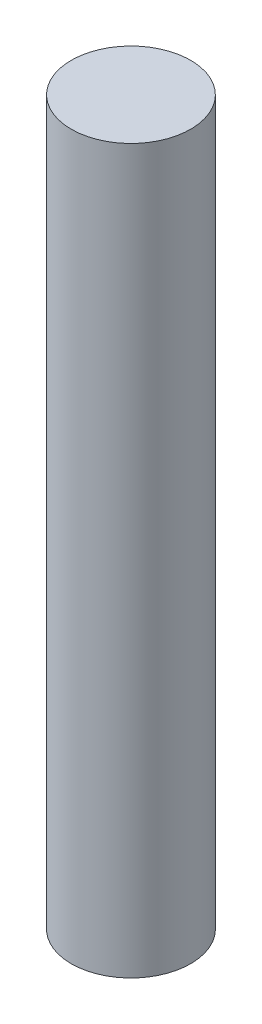
SolidWorks part; units mm, degrees
ref_plane "Front Plane" through (0, 0, 0) normal (0, 0, 1) x (1, 0, 0)
ref_plane "Top Plane" through (0, 0, 0) normal (0, 1, 0) x (1, 0, 0)
ref_plane "Right Plane" through (0, 0, 0) normal (1, 0, 0) x (0, 0, -1)
sketch "Sketch1" plane through (0, 0, 0) normal (0, 1, 0) x (1, 0, 0)
  circle A0 centre (0, 0) radius 9.5
  dimension "D1" = 19
extrude "Boss-Extrude1" add sketch "Sketch1" along normal blind 115
sketch "Sketch2" plane through (0, 0, 0) normal (0, -1, 0) x (1, 0, 0)
  line L1 (1.6108, 2.79) -> (-1.6108, 2.79)
  line L2 (-1.6108, 2.79) -> (-3.2216, 0)
  line L3 (-3.2216, 0) -> (-1.6108, -2.79)
  line L4 (-1.6108, -2.79) -> (1.6108, -2.79)
  line L5 (1.6108, -2.79) -> (3.2216, 0)
  line L6 (3.2216, 0) -> (1.6108, 2.79)
  circle A0 centre (0, 0) radius 2.79 construction
  dimension "D1" = 5.58
extrude "Cut-Extrude1" cut sketch "Sketch2" against normal blind 6.6
sketch3d "3DSketch1"
  line L0 (0, 0, 0) -> (0, 115, 0)
  line L1 (0, 115, 0) -> (0, 0, 0) construction
